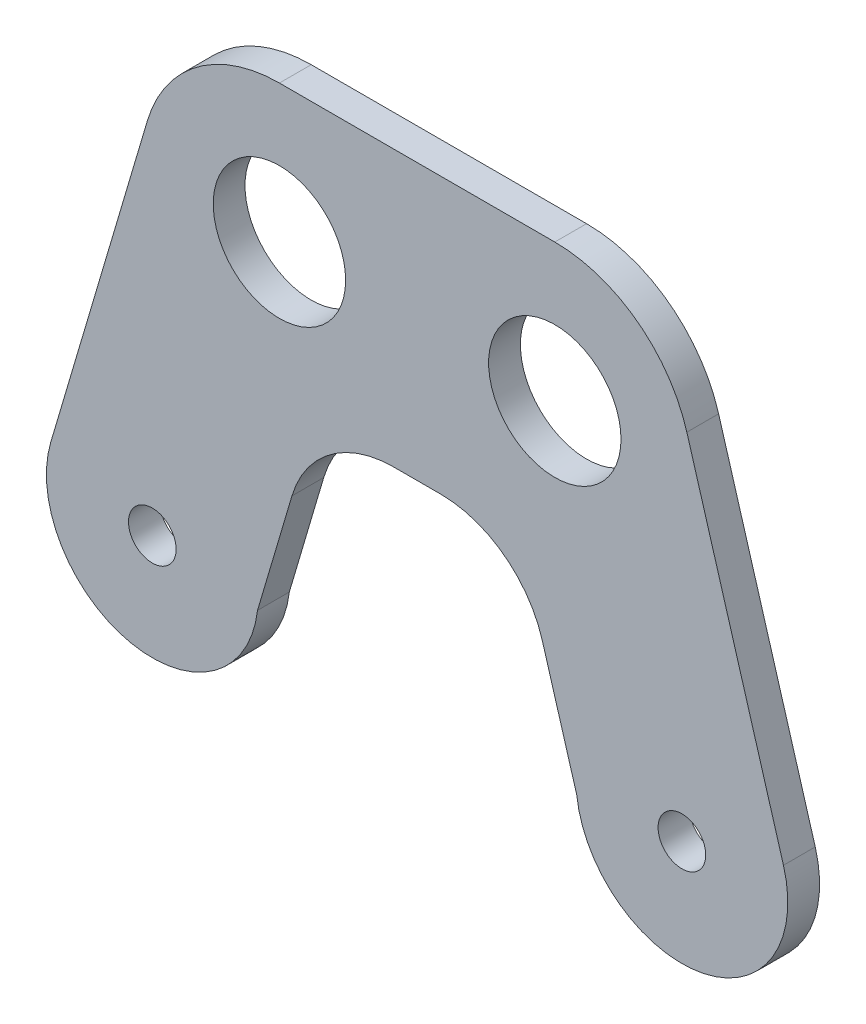
SolidWorks part; units mm, degrees
ref_plane "Plan de face" through (0, 0, 0) normal (0, 0, 1) x (1, 0, 0)
ref_plane "Plan de dessus" through (0, 0, 0) normal (0, 1, 0) x (1, 0, 0)
ref_plane "Plan de droite" through (0, 0, 0) normal (1, 0, 0) x (0, 0, -1)
sketch "Esquisse1" plane through (0, 0, 0) normal (0, 0, 1) x (1, 0, 0)
  line L0 (0, 0) -> (50, 0) construction
  line L1 (12, 30) -> (38, 30) construction
  line L2 (12, 30) -> (38, 30) construction
  line L3 (12, 43) -> (38, 43)
  line L4 (12, 17) -> (38, 17)
  circle A0 centre (0, 0) radius 2.25
  circle A1 centre (50, 0) radius 2.25
  circle A2 centre (12, 30) radius 6.25
  circle A3 centre (38, 30) radius 6.25
  circle A4 centre (0, 0) radius 10
  arc A5 (12, 43) -> (12, 17) centre (12, 30) ccw
  arc A6 (38, 17) -> (38, 43) centre (38, 30) ccw
  circle A7 centre (50, 0) radius 10
  point P9 (25, 30)
  dimension "D1" = 4.5
  dimension "D3" = 12.5
  dimension "D7" = 20
  dimension "D2" = 30
  dimension "D4" = 26
  dimension "D5" = 12
  dimension "D6" = 12
  dimension "D8" = 26
extrude "Boss.-Extru.1" add sketch "Esquisse1" along normal blind 3
sketch "Esquisse2" plane through (0, 0, 3) normal (0, 0, 1) x (1, 0, 0)
  line L0 (-0.4663, 33.6865) -> (-9.5895, 2.8358)
  line L1 (8.9629, -4.4347) -> (15.3016, 17)
  line L2 (12, 17) -> (38, 17) construction
  line L3 (25, 17) -> (25, 43) construction
  line L4 (38, 43) -> (12, 43) construction
  line L5 (12, 17) -> (15.3016, 17)
  line L6 (38, 17) -> (34.6984, 17)
  line L7 (41.0371, -4.4347) -> (34.6984, 17)
  line L8 (50.4663, 33.6865) -> (59.5895, 2.8358)
  arc A0 (12, 43) -> (12, 17) centre (12, 30) ccw construction
  circle A1 centre (0, 0) radius 10 construction
  arc A2 (8.9629, -4.4347) -> (-9.5895, 2.8358) centre (0, 0) ccw
  arc A3 (-0.4663, 33.6865) -> (12, 17) centre (12, 30) ccw
  arc A4 (50.4663, 33.6865) -> (38, 17) centre (38, 30) cw
  arc A5 (41.0371, -4.4347) -> (59.5895, 2.8358) centre (50, 0) cw
  arc M4 (12, 43) -> (12, 17) centre (12, 30) ccw
  line M5 (12, 17) -> (38, 17)
  arc M6 (38, 17) -> (38, 43) centre (38, 30) ccw
extrude "Boss.-Extru.2" add sketch "Esquisse2" against normal blind 3 contours A2 L1 L0 M5 M4 | L7 A5 L8 M6 M5
fillet "Congé1" radius 10 2 edges at (34.6984, 17, 1.5) (15.3016, 17, 1.5)
